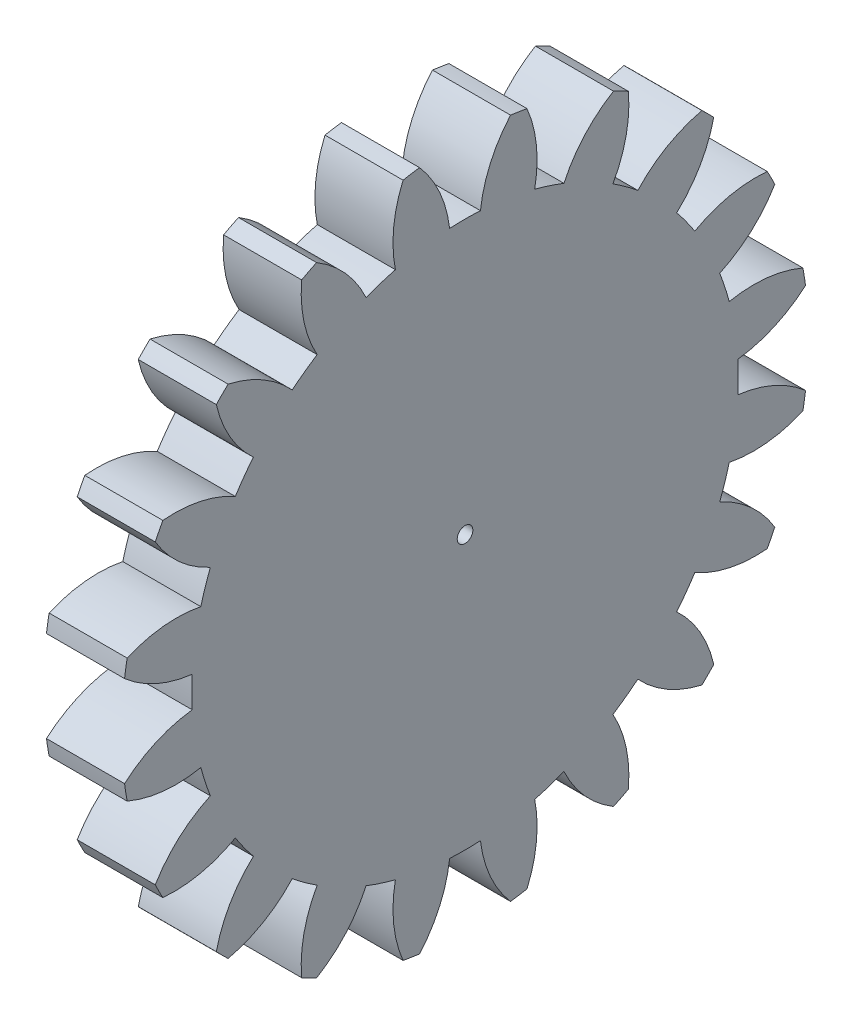
SolidWorks part; units mm, degrees
ref_plane "Plane1" through (0, 0, 0) normal (0, 0, 1) x (1, 0, 0)
ref_plane "Plane2" through (0, 0, 0) normal (0, 1, 0) x (1, 0, 0)
ref_plane "Plane3" through (0, 0, 0) normal (1, 0, 0) x (0, 0, -1)
other "Configuration Table"
sketch "HoldingSke" plane through (0, 0, 0) normal (0, 1, 0) x (1, 0, 0)
  line L0 (0, 0) -> (0.4698, -0.171)
  line L1 (-15, 0) -> (100, 0) construction
  line L2 (0, 0) -> (-2.1039, 2.3779)
  line L3 (0, 0) -> (-11.863, 4.5341)
  line L4 (0, 0) -> (8.1152, 2.9537)
  line L5 (0, 0) -> (-46.8476, -17.4728)
  line L6 (0, 0) -> (-4.1448, -2.7965)
  line L7 (-2.1039, 2.3779) -> (8.6586, 51.2059)
  line L8 (-76.2, 54.61) -> (-76.1, 54.61)
  line L9 (-71.009, 38.7566) -> (-53.1078, 45.2721)
  line L10 (-76.2, 71.12) -> (104.1128, 71.12)
  line L11 (0, 0) -> (-5, 0)
  line L12 (-76.2, 101.6) -> (-76.133, 101.6)
  line L13 (24.9733, 27.94) -> (52.9518, 28.4284)
  line L14 (24.9733, 27.94) -> (24.9743, 27.94)
  line L15 (24.9733, 27.94) -> (100.4006, 29.5858)
  line L16 (-63.627, -2) -> (-12.827, -2)
  circle A0 centre (0, 0) radius 0.5
  circle A1 centre (0, 0) radius 17.499
  circle A2 centre (0, 0) radius 37.5
  circle A3 centre (0, 0) radius 0.5
  dimension "MHD" = 34.998
  dimension "Hub_dia" = 75
  dimension "Bore" = 1
  dimension "MBD" = 1
  dimension "Num_teeth" = 20
  dimension "Pitch" = 0.5
  dimension "Overall_len" = 50
  dimension "Show_teeth" = 20
  dimension "Thickness" = 5
  dimension "OAL" = 50.0001
  dimension "T_dim" = 0.1
  dimension "Ap" = 20
  dimension "H" = 19.05
  dimension "Pitch_radius" = 180.3128
  dimension "Width" = 5
  dimension "Backlash" = 0.067
  dimension "Addendum_fac" = 1
  dimension "Dedendum_fac" = 1.25
  dimension "Clearance_fac" = 0.25
  dimension "Dedendum_add" = 0.001
  dimension "Module" = 2
sketch "BasProSke" plane through (0, 0, 0) normal (0, 1, 0) x (1, 0, 0)
  line L0 (-10, 0) -> (60, 0) construction
  line L1 (0, 0) -> (0, 22)
  line L2 (0, 0) -> (5, 0)
  line L3 (5, 0) -> (5, 22)
  line L4 (5, 22) -> (0, 22)
  dimension "Thickness" = 5
  dimension "Diameter" = 44
revolve "Base-Revolve" add sketch "BasProSke" angle 360 about L0
sketch "TooCutSke" plane through (0, 0, 0) normal (1, 0, 0) x (0, 0, -1)
  line L1 (0, 0) -> (0, 107) construction
  line L2 (0, 0) -> (-1.6864, 19.9288) construction
  line L3 (0, 0) -> (-6.2409, 39.4033) construction
  line L4 (-1.6864, 19.9288) -> (-3.1204, 19.7016) construction
  arc A0 (0.9862, 17.4712) -> (-0.9862, 17.4712) centre (0, 0) ccw
  arc A1 (2.9329, 21.8293) -> (-2.9329, 21.8293) centre (0, 0) ccw
  circle A2 centre (0, 0) radius 20 construction
  circle A3 centre (0, 0) radius 18.7939 construction
  arc A4 (-0.9862, 17.4712) -> (-2.9329, 21.8293) centre (-8.9313, 16.536) ccw
  arc A5 (2.9329, 21.8293) -> (0.9862, 17.4712) centre (8.9313, 16.536) ccw
  dimension "Root_dia" = 34.998
  dimension "Overcut_dia" = 44.0508
  dimension "Pitch_dia" = 40
  dimension "Base_dia" = 37.5877
  dimension "Flank_rad" = 8
  dimension "Half_ang" = 9
  dimension "Half_CT" = 1.4519
extrude "ToothCut" cut sketch "TooCutSke" along normal through all
fillet "Breaks" [suppressed] radius 0.04
fillet "RootFillets" [suppressed] radius 0.501
pattern_circular "TeethCuts" count 20 every 18 about axis through (-10, 0, 0) along (1, 0, 0) of "ToothCut", "RootFillets", "Breaks"
sketch "HubNeaOneSke" plane through (0, 0, 0) normal (-1, 0, 0) x (0, 0, 1)
  circle A0 centre (0, 0) radius 17.499
  dimension "Diameter" = 34.998
extrude "HubNearOne" [suppressed] add sketch "HubNeaOneSke" along normal blind 45.0001
sketch "HubNeaBotSke" plane through (0, 0, 0) normal (-1, 0, 0) x (0, 0, 1)
  circle A0 centre (0, 0) radius 17.499
  dimension "Diameter" = 34.998
extrude "HubNearBoth" [suppressed] add sketch "HubNeaBotSke" along normal blind 22.5
ref_plane "FarPln" through (5, 0, 0) normal (1, 0, 0) x (0, 0, -1)
sketch "HubFarSke" plane through (5, 0, 0) normal (1, 0, 0) x (0, 0, -1)
  circle A0 centre (0, 0) radius 17.499
  dimension "Diameter" = 34.998
extrude "HubFar" [suppressed] add sketch "HubFarSke" along normal blind 22.5
sketch "BorSke" plane through (0, 0, 0) normal (1, 0, 0) x (0, 0, -1)
  circle A0 centre (0, 0) radius 0.5
  dimension "Diameter" = 1
extrude "Bore" cut sketch "BorSke" along normal mid plane 100.0001
sketch "KeySke" plane through (0, 0, 0) normal (1, 0, 0) x (0, 0, -1)
  line L0 (-0.05, 0) -> (-0.05, 0.6)
  line L1 (-0.05, 0.6) -> (0.05, 0.6)
  line L2 (0.05, 0.6) -> (0.05, 0)
  line L3 (0, 0) -> (0, 34) construction
  line L4 (-0.05, 0) -> (0.05, 0)
  dimension "Offset" = 0.6
  dimension "Width" = 0.1
extrude "Keyway" [suppressed] cut sketch "KeySke" along normal mid plane 100.0001
pattern_circular "Keyway2" [suppressed] count 2 every 90 about axis through (-10, 0, 0) along (1, 0, 0)
equation "' \"Module@HoldingSke\" = 6.35"
equation "' \"Num_teeth@HoldingSke\" = 12"
equation "' \"Ap@HoldingSke\" =  20"
equation "' \"Ap@HoldingSke\" = 20"
equation "' \"Width@HoldingSke\" = 0.5 * 25.4"
equation "' \"Hub_dia@HoldingSke\"= 1 * 25.4"
equation "' \"Hub_dia@HoldingSke\" = 1 * 25.4"
equation "' \"Overall_len@HoldingSke\" = 1.0 * 25.4"
equation "' \"Bore@HoldingSke\" = 0.75 * 25.4"
equation "' \"T_dim@HoldingSke\" = 0.1 * 25.4"
equation "' \"Width@KeySke\" = 0.25 * 25.4"
equation "' \"Show_teeth@HoldingSke\" = 13"
equation "' \"Backlash@HoldingSke\" = 0.009 * 25.4"
equation "' \"Addendum_fac@HoldingSke\" = 1.0"
equation "' \"Dedendum_fac@HoldingSke\" = 1.25"
equation "' \"Dedendum_add@HoldingSke\" = 0.00005 * 25.4"
equation "' \"Clearance_fac@HoldingSke\" = 0.25"
equation "\"Pitch@HoldingSke\" = 1 / \"Module@HoldingSke\""
equation "\"Overcut_dia@TooCutSke\" = (\"Num_teeth@HoldingSke\" + 2 * \"Addendum_fac@HoldingSke\") / \"Pitch@HoldingSke\" + 0.002 * 25.4"
equation "\"Pitch_dia@TooCutSke\" = \"Num_teeth@HoldingSke\" / \"Pitch@HoldingSke\""
equation "\"Base_dia@TooCutSke\" = \"Num_teeth@HoldingSke\" / \"Pitch@HoldingSke\" * cos((\"Ap@HoldingSke\"  * 3.14159265 / 180))"
equation "\"Root_dia@TooCutSke\" = (\"Num_teeth@HoldingSke\" + 2) / \"Pitch@HoldingSke\" - 2 * (\"Addendum_fac@HoldingSke\" + \"Dedendum_fac@HoldingSke\") / \"Pitch@HoldingSke\" - \"Dedendum_add@HoldingSke\" * 2"
equation "\"Half_ang@TooCutSke\" = 180 / \"Num_teeth@HoldingSke\""
equation "\"Half_CT@TooCutSke\" = \"Num_teeth@HoldingSke\" / \"Pitch@HoldingSke\" * sin((3.14159265 / 2 / \"Num_teeth@HoldingSke\")) / 2 - 7 * \"Backlash@HoldingSke\" / 4"
equation "\"Flank_rad@TooCutSke\" = \"Num_teeth@HoldingSke\" / \"Pitch@HoldingSke\" / 5"
equation "\"Radius@RootFillets\" = \"Clearance_fac@HoldingSke\" / \"Pitch@HoldingSke\" + \"Dedendum_add@HoldingSke\""
equation "\"Break_rad@Breaks\" = 0.02 / \"Pitch@HoldingSke\""
equation "\"Thickness@HoldingSke\" = \"Width@HoldingSke\""
equation "\"OAL@HoldingSke\" = \"Thickness@HoldingSke\""
equation "\"MHD@HoldingSke\" = (\"Num_teeth@HoldingSke\" + 2) / \"Pitch@HoldingSke\" - 2 * (\"Addendum_fac@HoldingSke\" + \"Dedendum_fac@HoldingSke\")  / \"Pitch@HoldingSke\" - \"Dedendum_add@HoldingSke\" * 2"
equation "\"MBD@HoldingSke\" = (\"Num_teeth@HoldingSke\" + 2) / \"Pitch@HoldingSke\" - 2 * (\"Addendum_fac@HoldingSke\" + \"Dedendum_fac@HoldingSke\")  / \"Pitch@HoldingSke\" - \"Dedendum_add@HoldingSke\" * 2 - 0.002 * 25.4"
equation "\"MHD@HoldingSke\" = ((sgn( \"MHD@HoldingSke\" - \"Hub_dia@HoldingSke\" )-1)*( \"MHD@HoldingSke\" - \"Hub_dia@HoldingSke\" ))/-2+ \"Hub_dia@HoldingSke\""
equation "\"MBD@HoldingSke\" = ((sgn( \"MBD@HoldingSke\" - \"Bore@HoldingSke\" )-1)*( \"MBD@HoldingSke\" - \"Bore@HoldingSke\" ))/-2+ \"Bore@HoldingSke\""
equation "\"OAL@HoldingSke\" = ((sgn( \"OAL@HoldingSke\" - \"Overall_len@HoldingSke\" )+1)*( \"OAL@HoldingSke\" - \"Overall_len@HoldingSke\" ))/2 + \"Overall_len@HoldingSke\" + 0.000002 * 25.4"
equation "\"Num_teeth@TeethCuts\" = int( \"Show_teeth@HoldingSke\" ) + 1"
equation "\"Num_teeth@TeethCuts\" = ((sgn( \"Num_teeth@TeethCuts\" - \"Num_teeth@HoldingSke\" )-1)*( \"Num_teeth@TeethCuts\" - \"Num_teeth@HoldingSke\" ))/-2+ \"Num_teeth@HoldingSke\""
equation "\"Num_teeth@TeethCuts\" = ((sgn( \"Num_teeth@TeethCuts\" - 2.0)+1)*( \"Num_teeth@TeethCuts\" - 2.0))/2 +2.0"
equation "\"Angle@TeethCuts\" = 360.0 / \"Num_teeth@HoldingSke\""
equation "\"Diameter@BasProSke\" = (\"Num_teeth@HoldingSke\" + 2 * \"Addendum_fac@HoldingSke\") / \"Pitch@HoldingSke\""
equation "\"Thickness@BasProSke\"  = \"Thickness@HoldingSke\""
equation "' \"Fillet_rad@BasProSke\" =  \"Thickness@HoldingSke\" * 0.05"
equation "' \"Fillet_rad@BasProSke\" = \"Thickness@HoldingSke\" * 0.05"
equation "\"MHD@HoldingSke\" = ((sgn( \"MHD@HoldingSke\" - \"Root_dia@TooCutSke\" )-1)*( \"MHD@HoldingSke\" - \"Root_dia@TooCutSke\" ))/-2+ \"Root_dia@TooCutSke\""
equation "\"Diameter@HubNeaOneSke\" = \"MHD@HoldingSke\""
equation "\"Length@HubNearOne\" = \"OAL@HoldingSke\" - \"Thickness@BasProSke\""
equation "\"Diameter@HubNeaBotSke\" = \"MHD@HoldingSke\""
equation "\"Length@HubNearBoth\" = ( \"OAL@HoldingSke\" - \"Thickness@BasProSke\" ) / 2.0"
equation "\"Thickness@FarPln\" = \"Thickness@BasProSke\""
equation "\"Diameter@HubFarSke\" = \"MHD@HoldingSke\""
equation "\"Length@HubFar\" = ( \"OAL@HoldingSke\" - \"Thickness@BasProSke\" ) / 2.0"
equation "\"Diameter@BorSke\" = \"MBD@HoldingSke\""
equation "\"D1@Bore\" = \"OAL@HoldingSke\" * 2.0"
equation "\"D1@Keyway\" = \"OAL@HoldingSke\" * 2.0"
equation "\"Offset@KeySke\" = \"T_dim@HoldingSke\" + \"MBD@HoldingSke\" / 2.0"
